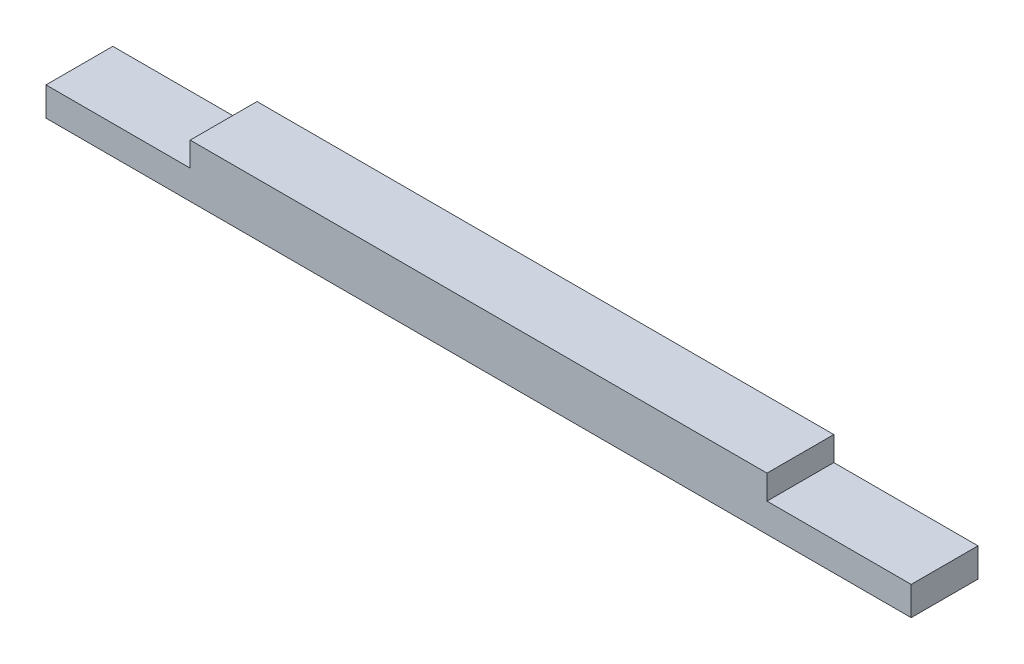
SolidWorks part; units mm, degrees
ref_plane "Front Plane" through (0, 0, 0) normal (0, 0, 1) x (1, 0, 0)
ref_plane "Top Plane" through (0, 0, 0) normal (0, 1, 0) x (1, 0, 0)
ref_plane "Right Plane" through (0, 0, 0) normal (1, 0, 0) x (0, 0, -1)
sketch "Sketch1" plane through (0, 0, 0) normal (0, 0, 1) x (1, 0, 0)
  line L0 (37.5, 15.3392) -> (37.5, 5.525) construction
  line L1 (-7.5, 0) -> (82.5, 0)
  line L2 (7.5, 3) -> (7.5, 5.525)
  line L3 (7.5, 5.525) -> (67.5, 5.525)
  line L4 (67.5, 3) -> (67.5, 5.525)
  line L5 (37.5, 0) -> (37.5, -11.7807) construction
  line L8 (67.5, 3) -> (82.5, 3)
  line L9 (82.5, 0) -> (82.5, 3)
  line L12 (7.5, 3) -> (-7.5, 3)
  line L13 (-7.5, 0) -> (-7.5, 3)
  point P14 (82.5, 1.5)
  dimension "D1" = 60
  dimension "D2" = 3
  dimension "D3" = 30
  dimension "D4" = 15
  dimension "D5" = 15
  dimension "D6" = 3
extrude "Boss-Extrude1" add sketch "Sketch1" along normal blind 6.95 contours L3 L4 L8 L9 L1 L13 L12 L2
